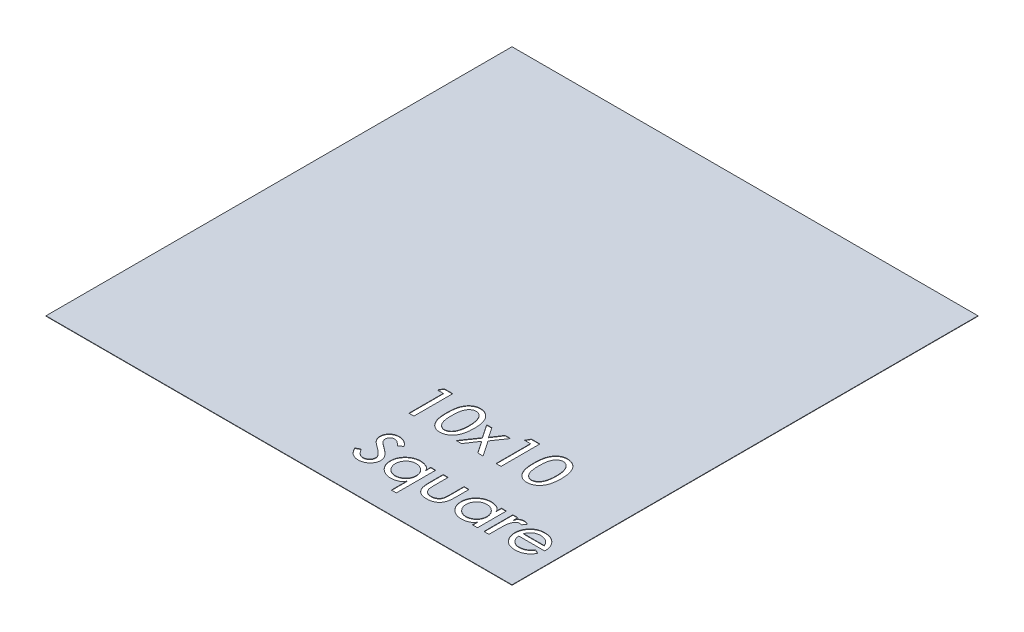
SolidWorks part; units mm, degrees
ref_plane "Front Plane" through (0, 0, 0) normal (0, 0, 1) x (1, 0, 0)
ref_plane "Top Plane" through (0, 0, 0) normal (0, 1, 0) x (1, 0, 0)
ref_plane "Right Plane" through (0, 0, 0) normal (1, 0, 0) x (0, 0, -1)
sketch "Sketch1" plane through (0, 0, 0) normal (0, 1, 0) x (1, 0, 0)
  line L1 (-1524, -1524) -> (1524, -1524)
  line L2 (-1524, -1524) -> (-1524, 1524)
  line L3 (-1524, 1524) -> (1524, 1524)
  line L4 (1524, -1524) -> (1524, 1524)
  line L5 (-1524, -1524) -> (1524, 1524) construction
  line L6 (-1524, 1524) -> (1524, -1524) construction
  point P0 (0, 0)
  dimension "D1" = 3048
extrude "Boss-Extrude1" add sketch "Sketch1" along normal blind 2.54
sketch "Sketch2" plane through (0, 2.54, 0) normal (0, 1, 0) x (1, 0, 0)
  line L0 (1524, -1524) -> (1524, 1524) construction
  line L1 (-1524, -1524) -> (1524, -1524) construction
  text T0 "<b>10x10</b>\r\n<b> Square</b>" font "Century Gothic" height 254
  dimension "D1" = 1397
  dimension "D2" = 635
extrude "Cut-Extrude2" cut sketch "Sketch2" against normal through all
